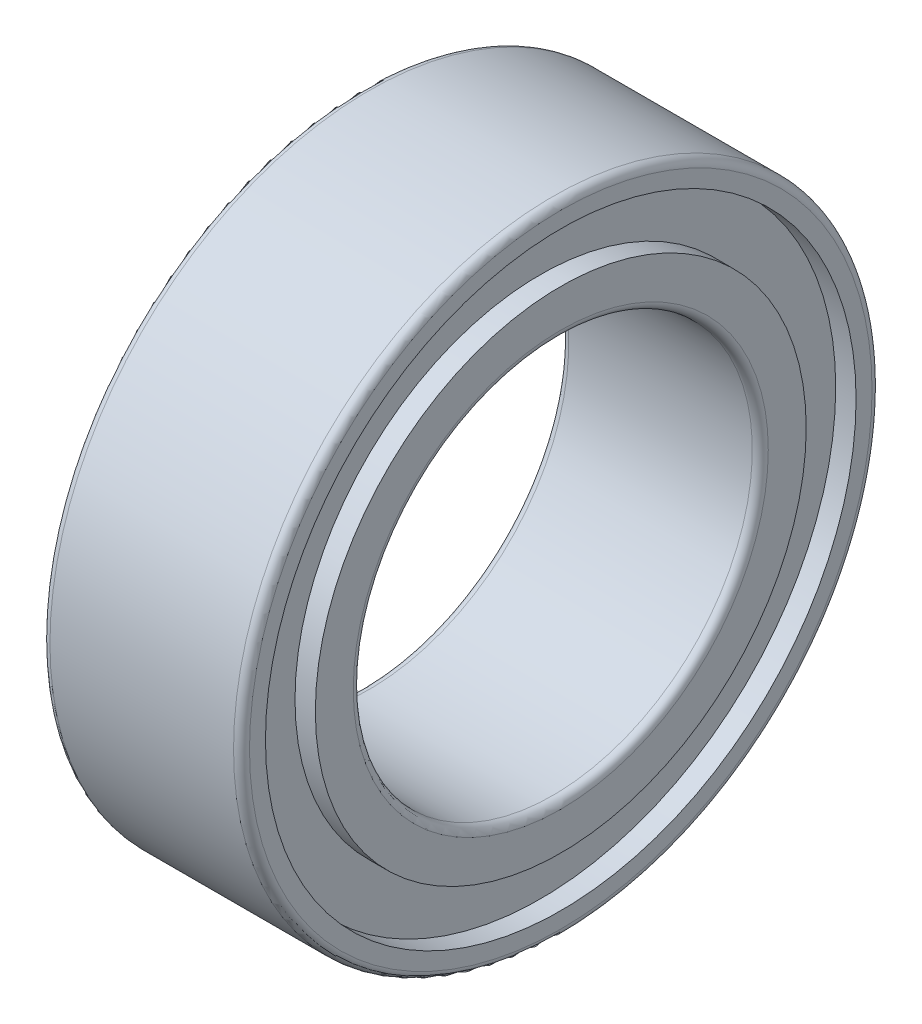
SolidWorks part; units mm, degrees
ref_plane "Front Plane" through (0, 0, 0) normal (0, 0, 1) x (1, 0, 0)
ref_plane "Top Plane" through (0, 0, 0) normal (0, 1, 0) x (1, 0, 0)
ref_plane "Right Plane" through (0, 0, 0) normal (1, 0, 0) x (0, 0, -1)
ref_plane "Plane1" through (0, 0, 0) normal (0, 0, 1) x (1, 0, 0)
sketch "Sketch1" plane through (0, 0, 0) normal (0, 0, 1) x (1, 0, 0)
  line L0 (0, 3.9) -> (0, 3.7)
  line L1 (0, 3.7) -> (0.255, 3.7)
  line L2 (0.255, 3.7) -> (0.255, 3.075)
  line L3 (0.255, 3.075) -> (0, 3.075)
  line L4 (0, 3.075) -> (0, 2.6)
  line L5 (0.1, 2.5) -> (2.4, 2.5)
  line L6 (2.5, 2.6) -> (2.5, 3.075)
  line L7 (2.5, 3.075) -> (2.245, 3.075)
  line L8 (2.245, 3.075) -> (2.245, 3.7)
  line L9 (2.245, 3.7) -> (2.5, 3.7)
  line L10 (2.5, 3.7) -> (2.5, 3.9)
  line L11 (2.4, 4) -> (0.1, 4)
  line L12 (2.4, 0) -> (0.1, 0) construction
  arc A0 (0, 2.6) -> (0.1, 2.5) centre (0.1, 2.6) ccw
  arc A1 (2.4, 2.5) -> (2.5, 2.6) centre (2.4, 2.6) ccw
  arc A2 (2.5, 3.9) -> (2.4, 4) centre (2.4, 3.9) ccw
  arc A3 (0.1, 4) -> (0, 3.9) centre (0.1, 3.9) ccw
revolve "Revolve1" add sketch "Sketch1" angle 360 about L12
